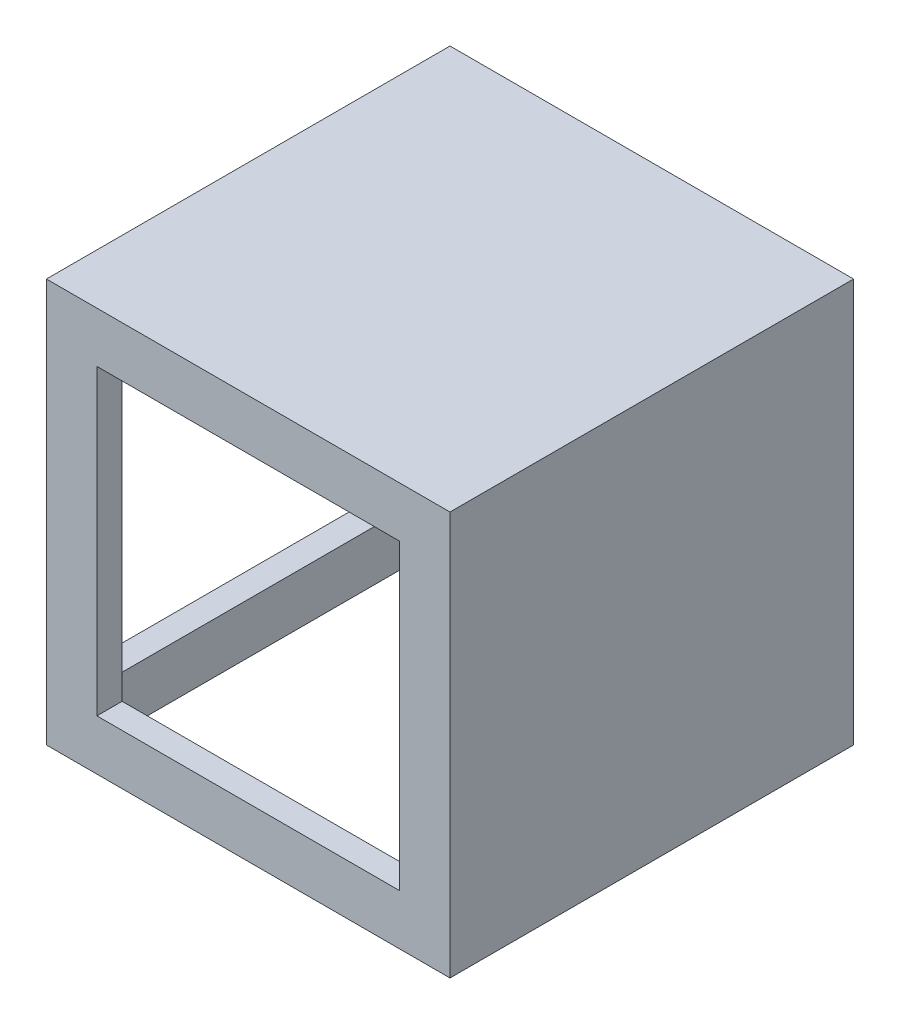
SolidWorks part; units mm, degrees
ref_plane "Front Plane" through (0, 0, 0) normal (0, 0, 1) x (1, 0, 0)
ref_plane "Top Plane" through (0, 0, 0) normal (0, 1, 0) x (1, 0, 0)
ref_plane "Right Plane" through (0, 0, 0) normal (1, 0, 0) x (0, 0, -1)
sketch "Sketch1" plane through (0, 0, 0) normal (0, 0, 1) x (1, 0, 0)
  line L0 (0, 0) -> (0, 16)
  line L1 (0, 16) -> (16, 16)
  line L2 (16, 16) -> (16, 0)
  line L3 (16, 0) -> (0, 0)
  dimension "D1" = 16
  dimension "D2" = 16
extrude "Boss-Extrude1" add sketch "Sketch1" along normal blind 16
shell "Shell1" thickness 1
sketch "Sketch2" plane through (0, 0, 0) normal (0, 0, -1) x (-1, 0, 0)
  line L0 (0, 0) -> (-16, 0) construction
  line L1 (-14, 14) -> (-2, 14)
  line L2 (-14, 14) -> (-14, 2)
  line L3 (-14, 2) -> (-2, 2)
  line L4 (-2, 14) -> (-2, 2)
  line L5 (-14, 14) -> (-2, 2) construction
  line L6 (-14, 2) -> (-2, 14) construction
  line L7 (0, 16) -> (0, 0) construction
  point P0 (-8, 8)
  dimension "D1" = 8
  dimension "D2" = 8
  dimension "D3" = 12
  dimension "D4" = 12
extrude "Cut-Extrude1" cut sketch "Sketch2" against normal through all
sketch "Sketch3" plane through (0, 0, 0) normal (-1, 0, 0) x (0, 0, 1)
  line L0 (16, 16) -> (16, 0) construction
  line L1 (2, 14) -> (14, 14)
  line L2 (2, 14) -> (2, 2)
  line L3 (2, 2) -> (14, 2)
  line L4 (14, 14) -> (14, 2)
  line L5 (2, 14) -> (14, 2) construction
  line L6 (2, 2) -> (14, 14) construction
  line L7 (16, 0) -> (0, 0) construction
  point P0 (8, 8)
  dimension "D1" = 8
  dimension "D2" = 8
  dimension "D3" = 12
  dimension "D4" = 12
extrude "Cut-Extrude3" cut sketch "Sketch3" against normal blind 7
